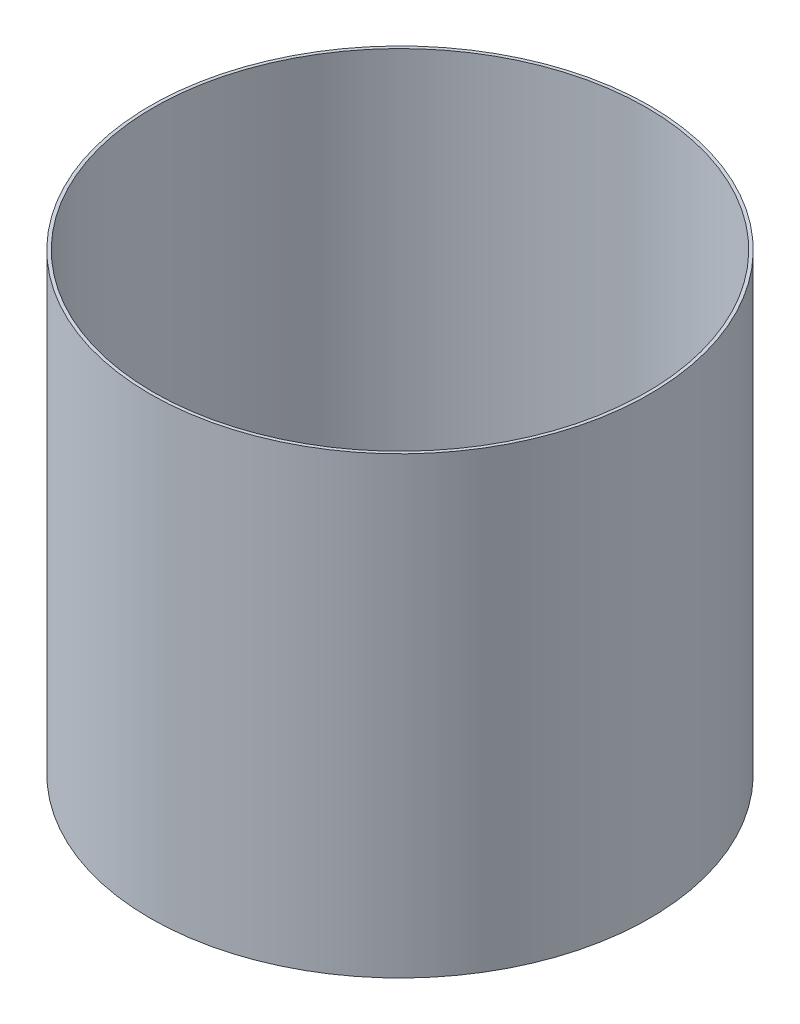
SolidWorks part; units mm, degrees
ref_plane "Front Plane" through (0, 0, 0) normal (0, 0, 1) x (1, 0, 0)
ref_plane "Top Plane" through (0, 0, 0) normal (0, 1, 0) x (1, 0, 0)
ref_plane "Right Plane" through (0, 0, 0) normal (1, 0, 0) x (0, 0, -1)
sketch "Sketch1" plane through (0, 0, 0) normal (0, 1, 0) x (1, 0, 0)
  circle A0 centre (0, 0) radius 130.175
  circle A1 centre (0, 0) radius 128.525
  dimension "D1" = 260.35
  dimension "D2" = 1.65
extrude "Boss-Extrude1" add sketch "Sketch1" along normal blind 234.95
sketch "Sketch2" plane through (0, 0, 0) normal (0, -1, 0) x (1, 0, 0)
  circle A0 centre (0, 0) radius 130.175 construction
  circle A2 centre (0, 0) radius 130.175
extrude "Boss-Extrude2" add sketch "Sketch2" along normal blind 1.65
sketch "Sketch3" plane through (0, -1.65, 0) normal (0, -1, 0) x (1, 0, 0)
  circle A0 centre (0, 0) radius 3.9688
  dimension "D1" = 7.9375
extrude "Cut-Extrude1" cut sketch "Sketch3" against normal through all
equation "\"BT\"=1.65"
equation "\"BD\"=260.35"
equation "\"D1@Sketch1\"=\"BD\""
equation "\"BH\"=234.95"
equation "\"D1@Boss-Extrude1\"=\"BH\""
equation "\"D1@Boss-Extrude2\"=\"BT\""
equation "\"D2@Sketch1\"=\"BT\""
